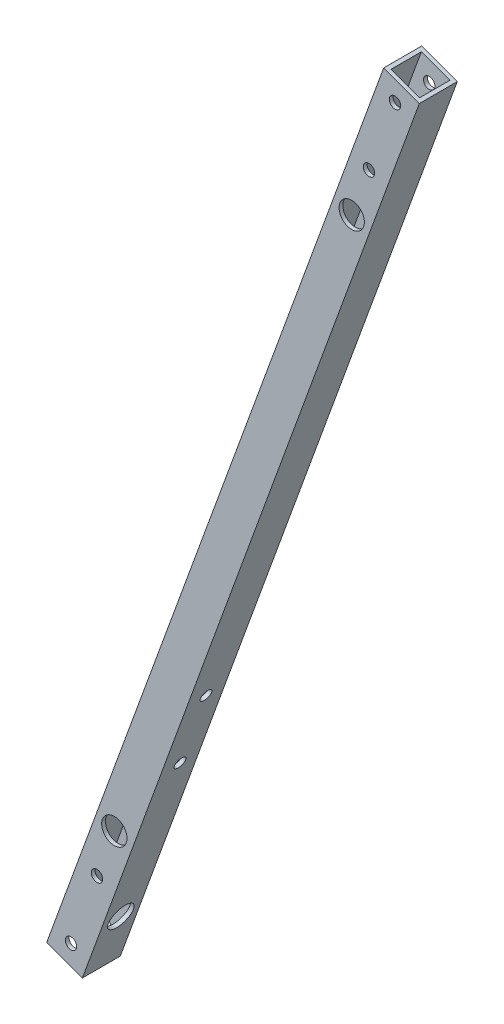
SolidWorks part; units mm, degrees
material "6063-T5"
ref_plane "正面" through (0, 0, 0) normal (0, 0, 1) x (1, 0, 0)
ref_plane "平面" through (0, 0, 0) normal (0, 1, 0) x (1, 0, 0)
ref_plane "右側面" through (0, 0, 0) normal (1, 0, 0) x (0, 0, -1)
sketch "ｽｹｯﾁ1" plane through (0, 0, 0) normal (0, 0, 1) x (1, 0, 0)
  line L0 (0, 0) -> (133.1152, 365.731) construction
  line L1 (133.1152, 365.731) -> (440, 0) construction
  line L2 (440, 0) -> (0, 0) construction
  line L3 (133.1152, 365.731) -> (133.1152, 0) construction
  line L4 (133.1152, 365.731) -> (0, 0)
  line L9 (133.1152, 365.731) -> (119.0198, 370.8613)
  line L11 (119.0198, 370.8613) -> (-14.0954, 5.1303)
  line L12 (-14.0954, 5.1303) -> (0, 0)
  dimension "D4" = 15
  dimension "D1" = 440
  dimension "D2" = 70
  dimension "D3" = 50
extrude "ﾎﾞｽ - 押し出し1" add sketch "ｽｹｯﾁ1" along normal blind 15
shell "ｼｪﾙ1" thickness 1.5
sketch "ｽｹｯﾁ6" plane through (0, 0, 15) normal (0, 0, 1) x (1, 0, 0)
  line L0 (133.1152, 365.731) -> (0, 0)
  line L1 (0, 0) -> (440, 0)
  line L2 (440, 0) -> (133.1152, 365.731)
  line L3 (42.3548, 116.369) -> (342.3548, 116.369)
  line L4 (42.3548, 116.369) -> (26.3922, 116.369)
  line L5 (119.0198, 370.8613) -> (-14.0954, 5.1303) construction
  line L6 (26.3922, 116.369) -> (24.6821, 111.6705)
  line L7 (24.6821, 111.6705) -> (38.7775, 106.5402)
  line L8 (38.7775, 106.5402) -> (42.3548, 116.369)
  line L9 (22.1169, 104.6228) -> (36.2123, 99.4925)
  dimension "D1" = 5
  dimension "D2" = 7.5
  dimension "D3" = 440
  dimension "D4" = 300
sketch "ｽｹｯﾁ3" plane through (0, 0, 15) normal (0, 0, 1) x (1, 0, 0)
  line L0 (133.1152, 365.731) -> (119.0198, 370.8613) construction
  line L2 (-7.0477, 2.5652) -> (126.0675, 368.2962) construction
  line L3 (-14.0954, 5.1303) -> (0, 0) construction
  circle A0 centre (-4.4825, 9.6128) radius 2.25
  circle A1 centre (123.5024, 361.2485) radius 2.25
  circle A2 centre (113.2418, 333.0577) radius 2.25
  circle A3 centre (5.7781, 37.8036) radius 2.25
  circle A4 centre (12.6185, 56.5975) radius 2.7
  circle A5 centre (106.4014, 314.2639) radius 2.7
  dimension "D1" = 7.5
  dimension "D2" = 30
  dimension "D3" = 4.5
  dimension "D4" = 4.5
  dimension "D5" = 4.5
  dimension "D6" = 30
  dimension "D7" = 5.4
  dimension "D8" = 7.5
  dimension "D9" = 4.5
  dimension "D12" = 5.4
  dimension "D10" = 20
  dimension "D11" = 20
extrude "ｶｯﾄ - 押し出し1" cut sketch "ｽｹｯﾁ3" against normal blind 25
sketch "ｽｹｯﾁ5" plane through (-14.0954, 5.1303, 0) normal (-0.9397, 0.342, 0) x (0, 0, 1)
  line L0 (0, 389.2028) -> (0, 0) construction
  line L1 (15, 0) -> (0, 0) construction
  circle A0 centre (7.5, 120.8777) radius 2.25
  circle A1 centre (7.5, 90.8777) radius 2.25
  circle A2 centre (7.5, 22.5) radius 2.7
  point P12 (7.5, 0)
  dimension "D1" = 7.5
  dimension "D3" = 4.5
  dimension "D4" = 4.5
  dimension "D5" = 30
  dimension "D6" = 15
  dimension "D7" = 22.5
  dimension "D8" = 5.4
  dimension "D2" = 7.5
extrude "ｶｯﾄ - 押し出し3" cut sketch "ｽｹｯﾁ5" against normal blind 20
hole_wizard "Ø10.0 (10) 直径の穴1" positions "ｽｹｯﾁ8" profile "ｽｹｯﾁ10" hole size "Ø10.0" standard "JIS"
sketch "ｽｹｯﾁ8" plane through (0, 0, 0) normal (0.9397, -0.342, 0) x (0, 0, -1)
  point P0 (-7.5, 22.5)
sketch "ｽｹｯﾁ10" plane through (7.6955, 21.1431, 7.5) normal (0, 0, 1) x (0.342, 0.9397, 0)
  line L0 (0, 0) -> (0, 1.5)
  line L1 (0, 1.5) -> (5, 1.5)
  line L2 (5, 1.5) -> (5, 0)
  line L5 (5, 0) -> (0, 0)
  line L10 (0, 1.5) -> (-5, 1.5) construction
  line L11 (0, -6.35) -> (0, 107.95) construction
  dimension "穴の直径" = 10
  dimension "穴の深さ" = 1.5
  dimension "ﾄﾞﾘﾙ角度" = 180
hole_wizard "Ø10.0 (10) 直径の穴2" positions "ｽｹｯﾁ11" profile "ｽｹｯﾁ12" hole size "Ø10.0" standard "JIS"
sketch "ｽｹｯﾁ11" plane through (0, 0, 15) normal (0, 0, 1) x (1, 0, 0)
  point P0 (106.4014, 314.2639)
  point P3 (12.6185, 56.5975)
sketch "ｽｹｯﾁ12" plane through (106.4014, 314.2639, 15) normal (1, 0, 0) x (0, -1, 0)
  line L0 (0, 0) -> (0, 1.5)
  line L1 (0, 1.5) -> (5, 1.5)
  line L2 (5, 1.5) -> (5, 0)
  line L5 (5, 0) -> (0, 0)
  line L10 (0, 1.5) -> (-5, 1.5) construction
  line L11 (0, -6.35) -> (0, 107.95) construction
  dimension "穴の直径" = 10
  dimension "穴の深さ" = 1.5
  dimension "ﾄﾞﾘﾙ角度" = 180
